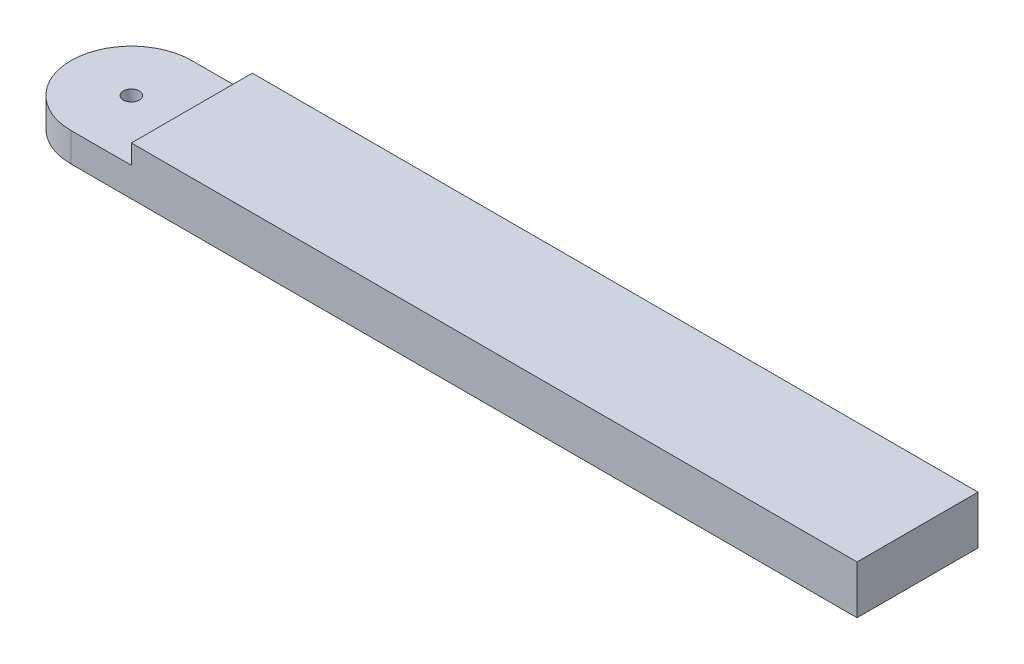
SolidWorks part; units mm, degrees
ref_plane "Front Plane" through (0, 0, 0) normal (0, 0, 1) x (1, 0, 0)
ref_plane "Top Plane" through (0, 0, 0) normal (0, 1, 0) x (1, 0, 0)
ref_plane "Right Plane" through (0, 0, 0) normal (1, 0, 0) x (0, 0, -1)
sketch "Sketch1" plane through (0, 0, 0) normal (0, 1, 0) x (1, 0, 0)
  line L1 (-41.5478, 10.4357) -> (120.9522, 10.4357)
  line L3 (-41.5478, -14.5643) -> (120.9522, -14.5643)
  line L4 (120.9522, 10.4357) -> (120.9522, -14.5643)
  arc A0 (-41.5478, 10.4357) -> (-41.5478, -14.5643) centre (-41.5478, -2.0643) ccw
  circle A1 centre (-41.5478, -2.0643) radius 1.65
  dimension "D3" = 25
extrude "Boss-Extrude1" add sketch "Sketch1" along normal blind 10
sketch "Sketch2" plane through (0, 10, 0) normal (0, 1, 0) x (1, 0, 0)
  line L0 (-41.5478, -14.5643) -> (120.9522, -14.5643) construction
  line L1 (-29.0478, -14.5643) -> (-58.5545, -14.5643)
  line L2 (-29.0478, -14.5643) -> (-29.0478, 15.5625)
  line L3 (-29.0478, 15.5625) -> (-58.5545, 15.5625)
  line L4 (-58.5545, -14.5643) -> (-58.5545, 15.5625)
  arc A0 (-41.5478, 10.4357) -> (-41.5478, -14.5643) centre (-41.5478, -2.0643) ccw construction
  point P6 (-54.0478, -2.0643)
  dimension "D1" = 25
extrude "Cut-Extrude1" cut sketch "Sketch2" against normal blind 4
